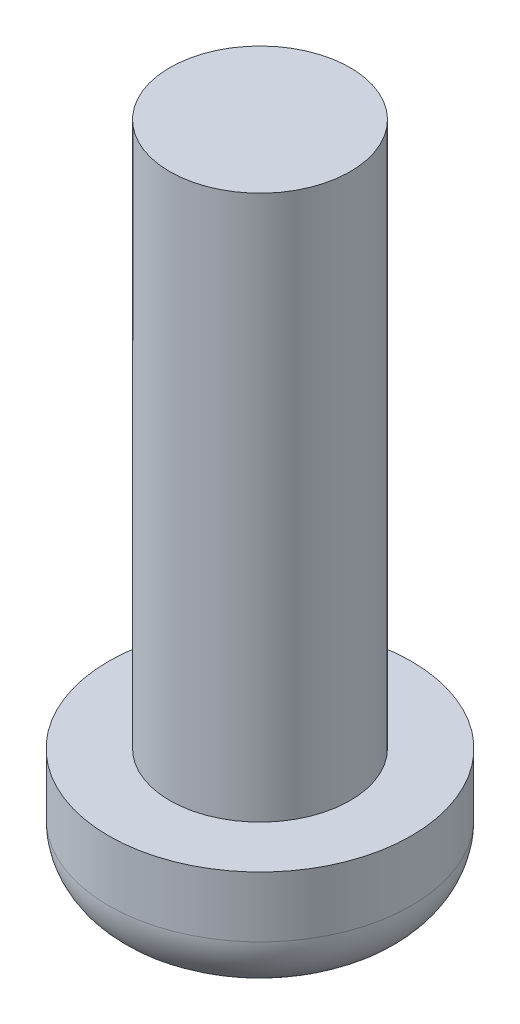
SolidWorks part; units mm, degrees
material "Plain Carbon Steel"
ref_plane "Front Plane" through (0, 0, 0) normal (0, 0, 1) x (1, 0, 0)
ref_plane "Top Plane" through (0, 0, 0) normal (0, 1, 0) x (1, 0, 0)
ref_plane "Right Plane" through (0, 0, 0) normal (1, 0, 0) x (0, 0, -1)
sketch "Sketch1" plane through (0, 0, 0) normal (0, 1, 0) x (1, 0, 0)
  circle A0 centre (0, 0) radius 2.5
  dimension "D1" = 5
extrude "Boss-Extrude1" add sketch "Sketch1" along normal blind 2 contours A0
sketch "Sketch2" plane through (0, 2, 0) normal (0, 1, 0) x (1, 0, 0)
  circle A0 centre (0, 0) radius 1.49
  dimension "D1" = 2.98
extrude "Boss-Extrude2" add sketch "Sketch2" along normal blind 9
fillet "Fillet3" radius 1 1 edges at (0, 0, 2.5)
